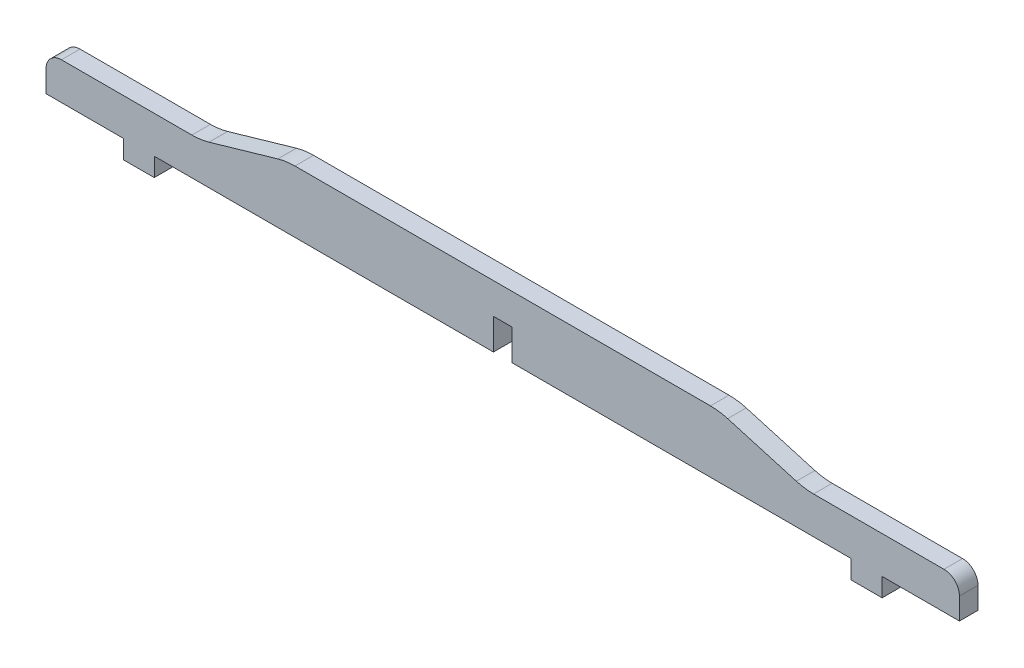
SolidWorks part; units mm, degrees
ref_plane "Front Plane" through (0, 0, 0) normal (0, 0, 1) x (1, 0, 0)
ref_plane "Top Plane" through (0, 0, 0) normal (0, 1, 0) x (1, 0, 0)
ref_plane "Right Plane" through (0, 0, 0) normal (1, 0, 0) x (0, 0, -1)
sketch "Sketch1" plane through (0, 0, 0) normal (0, 0, 1) x (1, 0, 0)
  line L0 (70, 0) -> (-70, 0)
  line L4 (112.6667, -20) -> (-112.6667, -20)
  line L5 (-147.6667, -20) -> (-122.6667, -20)
  line L6 (147.6667, -20) -> (122.6667, -20)
  line L7 (-122.6667, -20) -> (-122.6667, -26)
  line L8 (-122.6667, -26) -> (-112.6667, -26)
  line L9 (-112.6667, -26) -> (-112.6667, -20)
  line L10 (112.6667, -20) -> (112.6667, -26)
  line L11 (112.6667, -26) -> (122.6667, -26)
  line L12 (122.6667, -26) -> (122.6667, -20)
  line L13 (-147.6667, -20) -> (-147.6667, -8)
  line L14 (-147.6667, -8) -> (-97.6667, -8)
  line L15 (-97.6667, -8) -> (-70, 0)
  line L16 (70, 0) -> (97.6667, -8)
  line L17 (97.6667, -8) -> (147.6667, -8)
  line L18 (147.6667, -8) -> (147.6667, -20)
  point P4 (0, 0)
  point P10 (0, -20)
  point P19 (-73.5693, 0)
  point P21 (-61.0824, 0)
  point P22 (-60, 0)
  point P23 (-100.3794, -10)
  dimension "D1" = 295.3333
  dimension "D2" = 20
  dimension "D3" = 6
  dimension "D4" = 10
  dimension "D7" = 12
  dimension "D5" = 50
  dimension "D6" = 140
  dimension "D8" = 25
extrude "Boss-Extrude1" add sketch "Sketch1" along normal blind 6
fillet "Fillet1" radius 5 2 edges at (147.6667, -8, 3) (-147.6667, -8, 3)
fillet "Fillet2" radius 20 4 edges at (97.6667, -8, 3) (70, 0, 3) (-70, 0, 3) (-97.6667, -8, 3)
sketch "Sketch2" plane through (0, 0, 6) normal (0, 0, 1) x (1, 0, 0)
  line L0 (0, 0) -> (0, -20) construction
  line L1 (67.1665, 0) -> (-67.1665, 0) construction
  line L2 (-112.6667, -20) -> (112.6667, -20) construction
  line L4 (-3, -20) -> (3, -20)
  line L5 (-3, -20) -> (-3, -10)
  line L6 (-3, -10) -> (3, -10)
  line L7 (3, -20) -> (3, -10)
  point P10 (0, -10)
  dimension "D1" = 6
extrude "Cut-Extrude1" cut sketch "Sketch2" against normal through all both and the other way through all
equation "\"D1@Sketch1\"=300-4.66666666"
